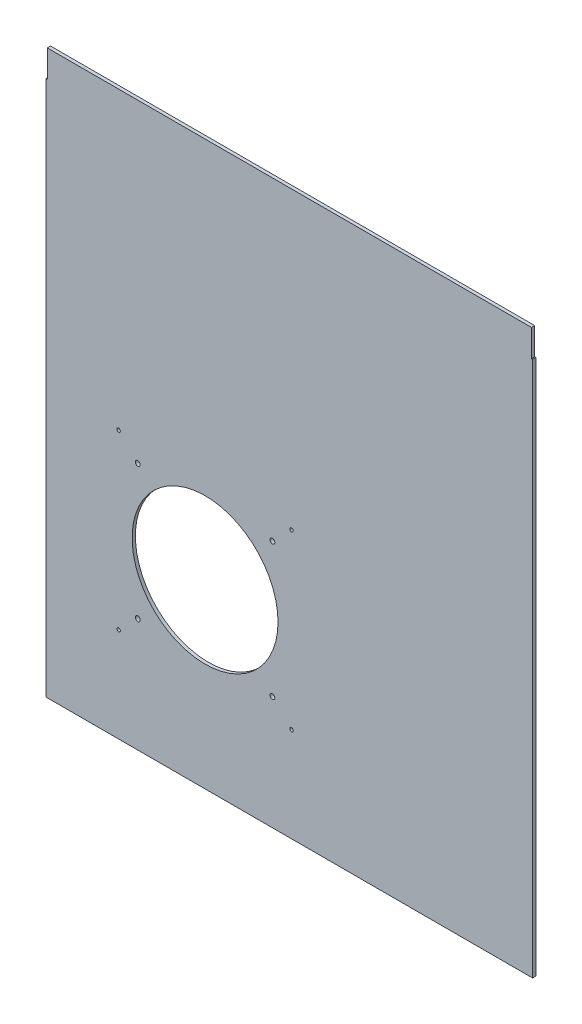
SolidWorks part; units mm, degrees
ref_plane "Alzado" through (0, 0, 0) normal (0, 0, 1) x (1, 0, 0)
ref_plane "Planta" through (0, 0, 0) normal (0, 1, 0) x (1, 0, 0)
ref_plane "Vista lateral" through (0, 0, 0) normal (1, 0, 0) x (0, 0, -1)
sketch "Croquis1" plane through (0, 0, 0) normal (0, 0, 1) x (1, 0, 0)
  line L0 (-261.8387, 298.7033) -> (-260.8387, 298.7033)
  line L1 (-260.8387, 323.7033) -> (187.1613, 323.7033)
  line L2 (-261.8387, 298.7033) -> (-261.8387, -197.0967)
  line L3 (-261.8387, -197.0967) -> (188.1613, -197.0967)
  line L4 (188.1613, 298.7033) -> (188.1613, -197.0967)
  line L5 (-260.8387, 298.7033) -> (-260.8387, 323.7033)
  line L6 (187.1613, 323.7033) -> (187.1613, 298.7033)
  line L7 (187.1613, 298.7033) -> (188.1613, 298.7033)
  dimension "D1" = 520.8
  dimension "D2" = 450
  dimension "D3" = 1
  dimension "D4" = 25
  dimension "D5" = 1
  dimension "D6" = 25
extrude "Saliente-Extruir1" add sketch "Croquis1" along normal blind 3
sketch "Croquis2" plane through (0, 0, 3) normal (0, 0, 1) x (1, 0, 0)
  line L0 (-261.8387, -197.0967) -> (188.1613, -197.0967) construction
  line L1 (-181.8387, 37.9033) -> (-47.8387, 37.9033) construction
  line L2 (-181.8387, 37.9033) -> (-181.8387, -97.0967) construction
  line L3 (-181.8387, -97.0967) -> (-47.8387, -97.0967) construction
  line L4 (-47.8387, 37.9033) -> (-47.8387, -97.0967) construction
  line L5 (-261.8387, 298.7033) -> (-261.8387, -197.0967) construction
  line L7 (-177.0887, -91.8467) -> (-52.5887, -91.8467) construction
  line L8 (-177.0887, -91.8467) -> (-177.0887, 32.6533) construction
  line L9 (-177.0887, 32.6533) -> (-52.5887, 32.6533) construction
  line L10 (-52.5887, -91.8467) -> (-52.5887, 32.6533) construction
  line L11 (-177.0887, -91.8467) -> (-52.5887, 32.6533) construction
  line L12 (-177.0887, 32.6533) -> (-52.5887, -91.8467) construction
  line L13 (-194.8387, -109.5967) -> (-34.8387, -109.5967) construction
  line L14 (-194.8387, -109.5967) -> (-194.8387, 50.4033) construction
  line L15 (-194.8387, 50.4033) -> (-34.8387, 50.4033) construction
  line L16 (-34.8387, -109.5967) -> (-34.8387, 50.4033) construction
  line L17 (-194.8387, -109.5967) -> (-34.8387, 50.4033) construction
  line L18 (-194.8387, 50.4033) -> (-34.8387, -109.5967) construction
  circle A0 centre (-114.8387, -29.5967) radius 67.5
  circle A1 centre (-52.5887, 32.6533) radius 2.25
  circle A5 centre (-34.8387, 50.4033) radius 1.6
  circle A6 centre (-52.5887, -91.8467) radius 2.25
  circle A7 centre (-34.8387, -109.5967) radius 1.6
  circle A8 centre (-177.0887, -91.8467) radius 2.25
  circle A9 centre (-194.8387, -109.5967) radius 1.6
  circle A10 centre (-177.0887, 32.6533) radius 2.25
  circle A11 centre (-194.8387, 50.4033) radius 1.6
  point P15 (-47.8387, -29.5967)
  point P17 (-114.8387, 37.9033)
  dimension "D6" = 4.5
  dimension "D9" = 3.2
  dimension "D1" = 134
  dimension "D2" = 135
  dimension "D3" = 100
  dimension "D4" = 80
  dimension "D5" = 124.5
  dimension "D8" = 160
  dimension "D7" = 4
extrude "Cortar-Extruir1" cut sketch "Croquis2" against normal up to vertex (3 mm away)
